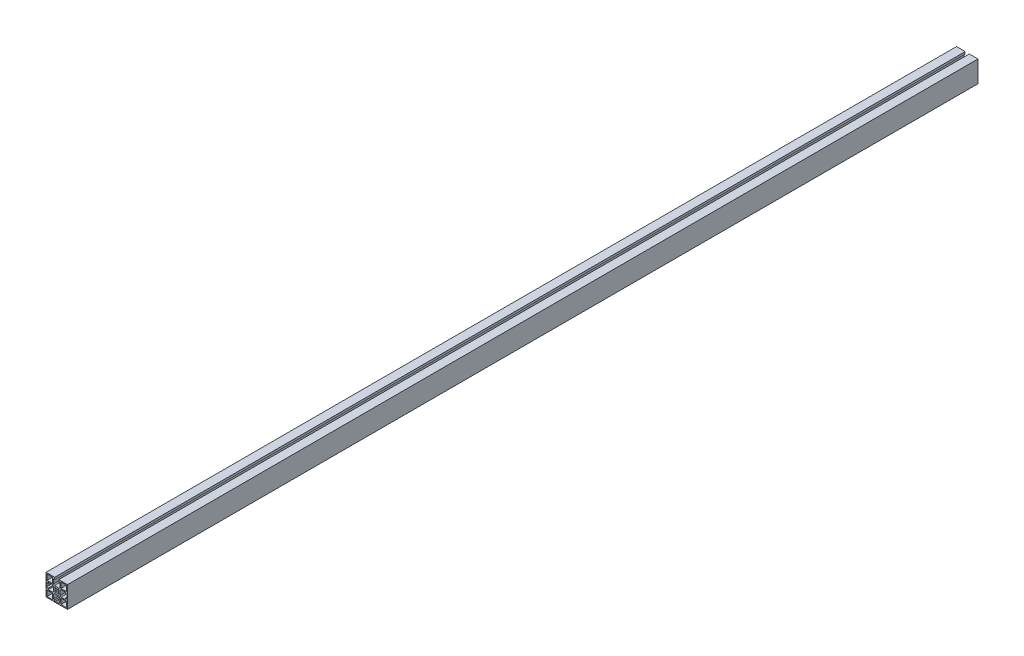
SolidWorks part; units mm, degrees
material "6061 Alloy"
ref_plane "Front Plane" through (0, 0, 0) normal (0, 0, 1) x (1, 0, 0)
ref_plane "Top Plane" through (0, 0, 0) normal (0, 1, 0) x (1, 0, 0)
ref_plane "Right Plane" through (0, 0, 0) normal (1, 0, 0) x (0, 0, -1)
sketch "Sketch1" plane through (0, 0, 0) normal (0, 0, 1) x (1, 0, 0)
  line L0 (-4.2495, 22.1993) -> (-4.2495, 22.4993)
  line L1 (-4.2495, 22.4993) -> (-4.2495, 22.1993)
  line L2 (4.2505, 22.1993) -> (4.2505, 22.4993)
  line L3 (4.2505, 22.4993) -> (4.2505, 22.1993)
  line L8 (-22.4995, -22.5007) -> (22.5005, -22.5007)
  line L9 (22.5005, -22.5007) -> (22.5005, 22.4993)
  line L10 (22.5005, 22.4993) -> (-22.4995, 22.4993)
  line L11 (-22.4995, 22.4993) -> (-22.4995, -22.5007)
  line L24 (-20.4995, -20.5007) -> (-20.4995, -8.8007)
  line L25 (-8.7996, -20.5007) -> (-20.4995, -20.5007)
  line L26 (-8.7996, -8.8007) -> (-8.7996, -20.5007)
  line L27 (-20.4995, -8.8007) -> (-8.7996, -8.8007)
  line L28 (8.8005, -20.5008) -> (8.8005, -8.8008)
  line L29 (20.5005, -20.5008) -> (8.8005, -20.5008)
  line L30 (20.5005, -8.8008) -> (20.5005, -20.5008)
  line L31 (8.8005, -8.8008) -> (20.5005, -8.8008)
  line L32 (20.5006, 8.7993) -> (8.8006, 8.7993)
  line L33 (20.5006, 20.4993) -> (20.5006, 8.7993)
  line L34 (8.8006, 20.4993) -> (20.5006, 20.4993)
  line L35 (8.8006, 8.7993) -> (8.8006, 20.4993)
  line L36 (-8.7995, 20.4993) -> (-8.7995, 8.7993)
  line L37 (-8.7995, 8.7993) -> (-20.4995, 8.7993)
  line L38 (-20.4995, 8.7993) -> (-20.4995, 20.4993)
  line L39 (-20.4995, 20.4993) -> (-8.7995, 20.4993)
  line L54 (-22.1995, -3.9507) -> (-21.7318, -3.483)
  line L55 (-22.1995, -4.2507) -> (-22.1995, -3.9507)
  line L56 (-17.9995, -4.2507) -> (-22.1995, -4.2507)
  line L57 (-17.9995, -6.8007) -> (-17.9995, -4.2507)
  line L58 (-9.1995, -6.8007) -> (-17.9995, -6.8007)
  line L59 (-7.1995, -4.8007) -> (-9.1995, -6.8007)
  line L60 (-7.1995, 4.7993) -> (-7.1995, -4.8007)
  line L61 (-9.1995, 6.7993) -> (-7.1995, 4.7993)
  line L62 (-17.9995, 6.7993) -> (-9.1995, 6.7993)
  line L63 (-17.9995, 4.2493) -> (-17.9995, 6.7993)
  line L64 (-22.1995, 4.2493) -> (-17.9995, 4.2493)
  line L65 (-22.1995, 3.9493) -> (-22.1995, 4.2493)
  line L66 (-21.7317, 3.4815) -> (-22.1995, 3.9493)
  line L67 (-20.9995, -1.7152) -> (-20.9995, 1.7137)
  line L82 (-6.7995, -18.0007) -> (-6.7995, -9.2007)
  line L83 (-4.2495, -18.0007) -> (-6.7995, -18.0007)
  line L84 (-4.2495, -22.2007) -> (-4.2495, -18.0007)
  line L85 (-3.9495, -22.2007) -> (-4.2495, -22.2007)
  line L86 (-3.4817, -21.733) -> (-3.9495, -22.2007)
  line L87 (1.715, -21.0007) -> (-1.7139, -21.0007)
  line L88 (3.9505, -22.2007) -> (3.4828, -21.733)
  line L89 (4.2505, -22.2007) -> (3.9505, -22.2007)
  line L90 (4.2505, -18.0007) -> (4.2505, -22.2007)
  line L91 (6.8005, -18.0007) -> (4.2505, -18.0007)
  line L92 (6.8005, -9.2007) -> (6.8005, -18.0007)
  line L93 (4.8005, -7.2007) -> (6.8005, -9.2007)
  line L94 (-4.7995, -7.2007) -> (4.8005, -7.2007)
  line L95 (-6.7995, -9.2007) -> (-4.7995, -7.2007)
  line L110 (7.2005, -4.8007) -> (7.2005, 4.7993)
  line L111 (9.2005, -6.8007) -> (7.2005, -4.8007)
  line L112 (18.0005, -6.8007) -> (9.2005, -6.8007)
  line L113 (18.0005, -4.2507) -> (18.0005, -6.8007)
  line L114 (22.2005, -4.2507) -> (18.0005, -4.2507)
  line L115 (22.2005, -3.9507) -> (22.2005, -4.2507)
  line L116 (21.7327, -3.4829) -> (22.2005, -3.9507)
  line L117 (21.0005, 1.7138) -> (21.0005, -1.7151)
  line L118 (22.2005, 3.9493) -> (21.7328, 3.4816)
  line L119 (22.2005, 4.2493) -> (22.2005, 3.9493)
  line L120 (18.0005, 4.2493) -> (22.2005, 4.2493)
  line L121 (18.0005, 6.7993) -> (18.0005, 4.2493)
  line L122 (9.2005, 6.7993) -> (18.0005, 6.7993)
  line L123 (7.2005, 4.7993) -> (9.2005, 6.7993)
  line L138 (-4.7995, 7.1993) -> (-6.7995, 9.1993)
  line L139 (4.8005, 7.1993) -> (-4.7995, 7.1993)
  line L140 (6.8005, 9.1993) -> (4.8005, 7.1993)
  line L141 (6.8005, 17.9993) -> (6.8005, 9.1993)
  line L142 (4.2505, 17.9993) -> (6.8005, 17.9993)
  line L143 (4.2505, 22.1993) -> (4.2505, 17.9993)
  line L144 (3.9505, 22.1993) -> (4.2505, 22.1993)
  line L145 (3.4828, 21.7316) -> (3.9505, 22.1993)
  line L146 (-1.7139, 20.9993) -> (1.715, 20.9993)
  line L147 (-3.9495, 22.1993) -> (-3.4817, 21.7315)
  line L148 (-4.2495, 22.1993) -> (-3.9495, 22.1993)
  line L149 (-4.2495, 17.9993) -> (-4.2495, 22.1993)
  line L150 (-6.7995, 17.9993) -> (-4.2495, 17.9993)
  line L151 (-6.7995, 9.1993) -> (-6.7995, 17.9993)
  line L164 (-4.5957, -3.1827) -> (-3.2622, -1.8492)
  line L165 (-3.1815, -4.5969) -> (-4.5957, -3.1827)
  line L166 (-1.848, -3.2635) -> (-3.1815, -4.5969)
  line L167 (3.1825, -4.5969) -> (1.849, -3.2635)
  line L168 (4.5967, -3.1827) -> (3.1825, -4.5969)
  line L169 (3.2633, -1.8492) -> (4.5967, -3.1827)
  line L170 (4.5967, 3.1813) -> (3.2633, 1.8478)
  line L171 (3.1825, 4.5955) -> (4.5967, 3.1813)
  line L172 (1.849, 3.262) -> (3.1825, 4.5955)
  line L173 (-3.1815, 4.5955) -> (-1.848, 3.262)
  line L174 (-4.5957, 3.1813) -> (-3.1815, 4.5955)
  line L175 (-3.2622, 1.8478) -> (-4.5957, 3.1813)
  arc A2 (-21.7318, -3.483) -> (-20.9995, -1.7152) centre (-23.4995, -1.7152) ccw
  arc A3 (-20.9995, 1.7137) -> (-21.7317, 3.4815) centre (-23.4995, 1.7137) ccw
  arc A6 (-1.7139, -21.0007) -> (-3.4817, -21.733) centre (-1.7139, -23.5007) ccw
  arc A7 (3.4828, -21.733) -> (1.715, -21.0007) centre (1.715, -23.5007) ccw
  arc A10 (21.0005, -1.7151) -> (21.7327, -3.4829) centre (23.5005, -1.7151) ccw
  arc A11 (21.7328, 3.4816) -> (21.0005, 1.7138) centre (23.5005, 1.7138) ccw
  arc A14 (1.715, 20.9993) -> (3.4828, 21.7316) centre (1.715, 23.4993) ccw
  arc A15 (-3.4817, 21.7315) -> (-1.7139, 20.9993) centre (-1.7139, 23.4993) ccw
  arc A20 (-1.848, -3.2635) -> (1.849, -3.2635) centre (0.0005, -0.0007) ccw
  arc A21 (3.2633, -1.8492) -> (3.2633, 1.8478) centre (0.0005, -0.0007) ccw
  arc A22 (1.849, 3.262) -> (-1.848, 3.262) centre (0.0005, -0.0007) ccw
  arc A23 (-3.2622, 1.8478) -> (-3.2622, -1.8492) centre (0.0005, -0.0007) ccw
extrude "Boss-Extrude1" add sketch "Sketch1" along normal blind 1907.794 contours L10 L11 L8 L9 A23 L175 L174 L173 A22 L172 L171 L170 A21 L169 L168 L167 A20 L166 L165 L164 L24 L27 L26 L25 L28 L31 L30 L29 L32 L35 L34 L33 L38 L39 L36 L37 L67 A3 L66 L65 L64 L63 L62 L61 L60
